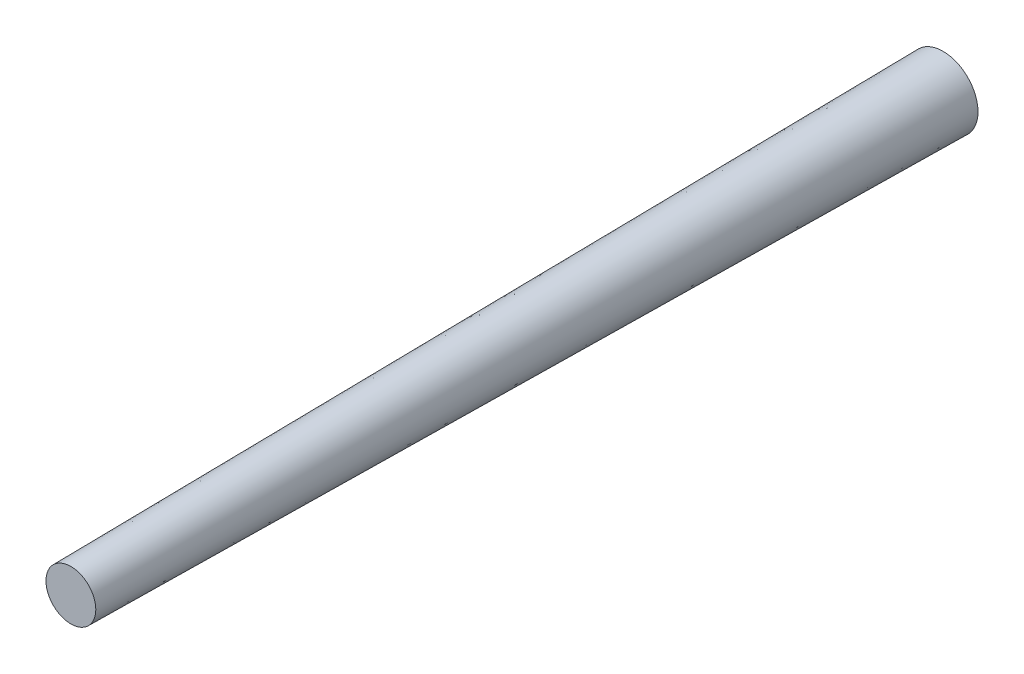
SolidWorks part; units mm, degrees
ref_plane "Front Plane" through (0, 0, 0) normal (0, 0, 1) x (1, 0, 0)
ref_plane "Top Plane" through (0, 0, 0) normal (0, 1, 0) x (1, 0, 0)
ref_plane "Right Plane" through (0, 0, 0) normal (1, 0, 0) x (0, 0, -1)
ref_plane "Plane1" through (0, 0, 88.9) normal (0, 0, 1) x (1, 0, 0)
sketch "Sketch2" plane through (0, 0, 0) normal (0, 0, 1) x (1, 0, 0)
  circle A0 centre (0, 0) radius 3.556
  dimension "D1" = 7.112
sketch "Sketch3" plane through (0, 0, 88.9) normal (0, 0, 1) x (1, 0, 0)
  circle A0 centre (0, 0) radius 2.54
  dimension "D1" = 5.08
loft "Loft1" add profiles "Sketch3", "Sketch2"
